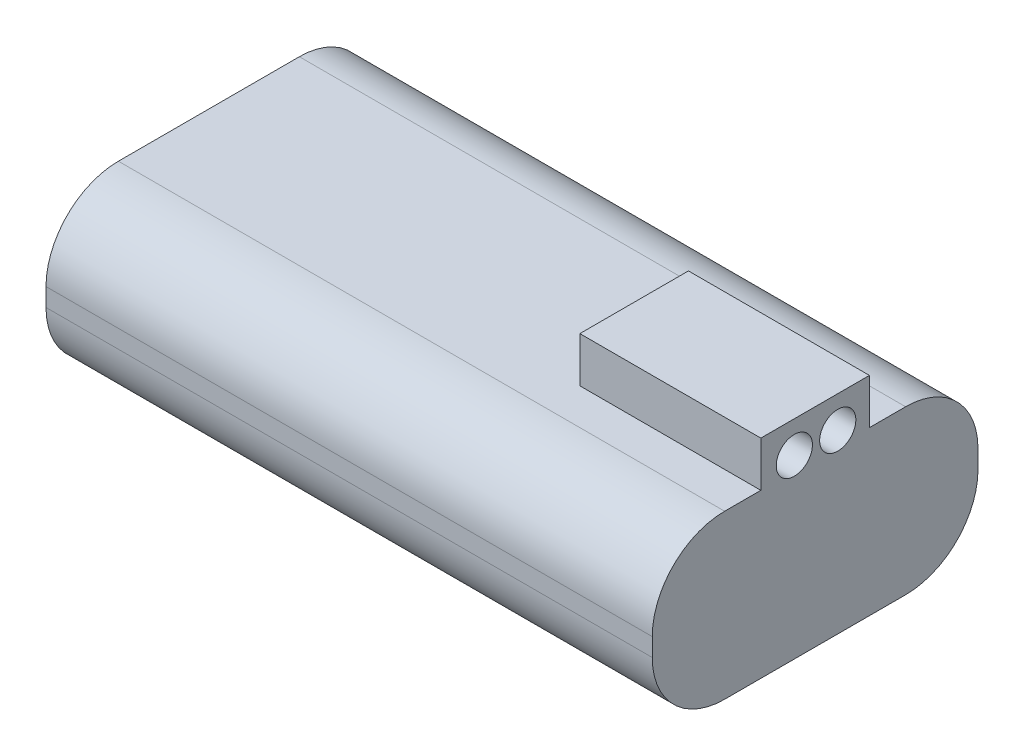
SolidWorks part; units mm, degrees
ref_plane "前视基准面" through (0, 0, 0) normal (0, 0, 1) x (1, 0, 0)
ref_plane "上视基准面" through (0, 0, 0) normal (0, 1, 0) x (1, 0, 0)
ref_plane "右视基准面" through (0, 0, 0) normal (1, 0, 0) x (0, 0, -1)
other "Configuration Table"
sketch "草图1" plane through (0, 0, 0) normal (0, 1, 0) x (1, 0, 0)
  line L1 (-33.5, -18) -> (33.5, -18)
  line L2 (-33.5, -18) -> (-33.5, 18)
  line L3 (-33.5, 18) -> (33.5, 18)
  line L4 (33.5, -18) -> (33.5, 18)
  line L5 (-33.5, -18) -> (33.5, 18) construction
  line L6 (-33.5, 18) -> (33.5, -18) construction
  point P0 (0, 0)
  dimension "D1" = 36
  dimension "D2" = 67
extrude "凸台-拉伸1" add sketch "草图1" along normal blind 18
sketch "草图2" plane through (0, 18, 0) normal (0, 1, 0) x (1, 0, 0)
  line L0 (13.5, 18) -> (13.5, -26.743) construction
  line L2 (33.5, -18) -> (33.5, 18) construction
  line L3 (0, 0) -> (43.926, 0) construction
  line L5 (13.5, 6) -> (33.5, 6)
  line L6 (13.5, 6) -> (13.5, -6)
  line L7 (13.5, -6) -> (33.5, -6)
  line L8 (33.5, 6) -> (33.5, -6)
  dimension "D1" = 20
  dimension "D2" = 12
extrude "凸台-拉伸2" add sketch "草图2" along normal blind 5
fillet "圆角1" radius 8 4 edges at (0, 0, -18) (0, 18, -18) (0, 0, 18) (0, 18, 18)
ref_plane "基准面1" through (33.5, 0, 0) normal (1, 0, 0) x (0, 0, -1)
sketch "草图3" plane through (33.5, 0, 0) normal (1, 0, 0) x (0, 0, -1)
  line L0 (6, 23) -> (6, 18) construction
  line L1 (-6, 23) -> (6, 23) construction
  circle A0 centre (2.5, 19.5) radius 2
  circle A1 centre (-2.3, 19.5) radius 2
  dimension "D1" = 4
  dimension "D2" = 3.5
  dimension "D3" = 3.5
  dimension "D4" = 4.8
extrude "切除-拉伸1" cut sketch "草图3" against normal blind 5
